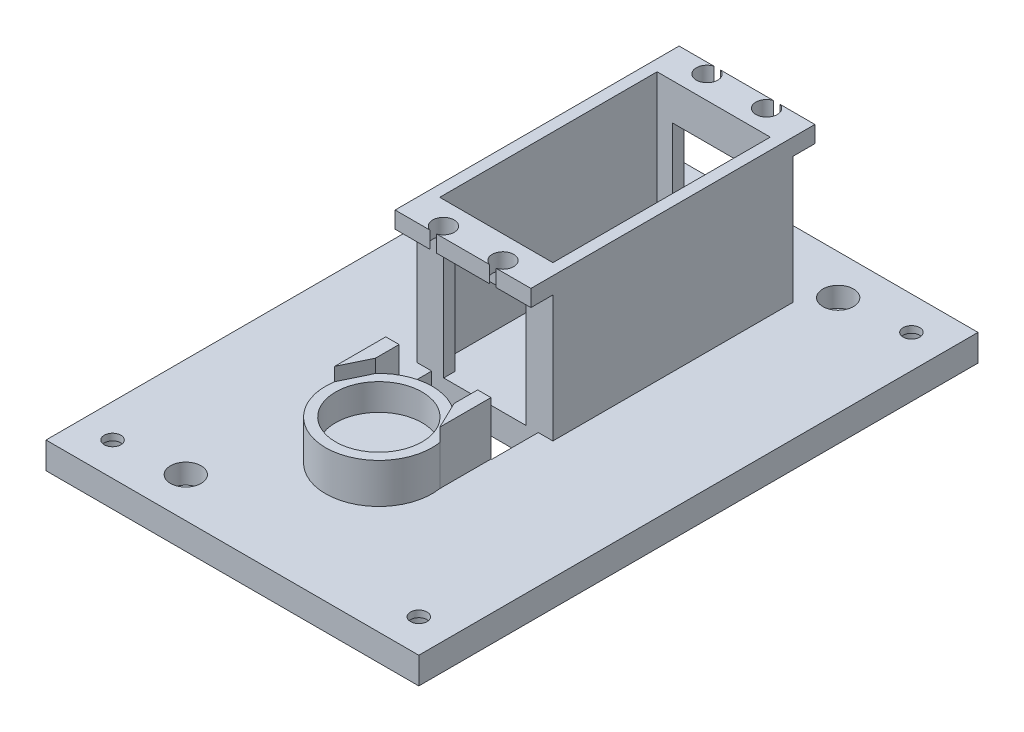
SolidWorks part; units mm, degrees
other "Markup1"
sketch "Sketch13" plane through (63.4306, 35.56, -46.9233) normal (0.8871, 0.4534, -0.0863) x (0.4601, -0.8836, 0.0876)
sketch "Sketch14" plane through (63.4306, 35.56, -46.9233) normal (0.8871, 0.4534, -0.0863) x (0.4601, -0.8836, 0.0876)
sketch "Sketch18" plane through (63.4306, 35.56, -46.9233) normal (0.8871, 0.4534, -0.0863) x (0.4601, -0.8836, 0.0876)
sketch "Sketch19" plane through (63.4306, 35.56, -46.9233) normal (0.8871, 0.4534, -0.0863) x (0.4601, -0.8836, 0.0876)
sketch "Sketch20" plane through (63.4306, 35.56, -46.9233) normal (0.8871, 0.4534, -0.0863) x (0.4601, -0.8836, 0.0876)
sketch "Sketch21" plane through (63.4306, 35.56, -46.9233) normal (0.8871, 0.4534, -0.0863) x (0.4601, -0.8836, 0.0876)
sketch "Sketch22" plane through (63.4306, 33.655, -46.9233) normal (0.8871, 0.4534, -0.0863) x (0.4601, -0.8836, 0.0876)
ref_plane "Front Plane" through (0, 0, 0) normal (0, 0, 1) x (1, 0, 0)
ref_plane "Top Plane" through (0, 0, 0) normal (0, 1, 0) x (1, 0, 0)
ref_plane "Right Plane" through (0, 0, 0) normal (1, 0, 0) x (0, 0, -1)
sketch "Sketch1" plane through (56.4019, 0, 2.6132) normal (0, 1, 0) x (1, 0, 0)
  line L1 (-64.0913, -57.1435) -> (7.0287, -57.1435)
  line L2 (-64.0913, -57.1435) -> (-64.0913, 49.5365)
  line L3 (-64.0913, 49.5365) -> (7.0287, 49.5365)
  line L4 (7.0287, -57.1435) -> (7.0287, 49.5365)
  dimension "D1" = 71.12
  dimension "D2" = 106.68
extrude "Boss-Extrude1" add sketch "Sketch1" along normal blind 5.08
sketch "Sketch3" plane through (56.4019, 5.08, 2.6132) normal (0, 1, 0) x (1, 0, 0)
  line L1 (-17.7363, 34.6775) -> (-39.3263, 34.6775)
  line L2 (-17.7363, 34.6775) -> (-17.7363, -6.8007)
  line L3 (-17.7363, -6.8007) -> (-39.3263, -6.8007)
  line L4 (-39.3263, 34.6775) -> (-39.3263, -6.8007)
  line L5 (-41.4853, 36.8365) -> (-15.5773, 36.8365)
  line L6 (-41.4853, 36.8365) -> (-41.4853, -8.9597)
  line L7 (-41.4853, -8.9597) -> (-15.5773, -8.9597)
  line L8 (-15.5773, 36.8365) -> (-15.5773, -8.9597)
  line L9 (7.0287, 49.5365) -> (-64.0913, 49.5365) construction
  point P5 (-28.5313, 36.8365)
  point P8 (-28.5313, 49.5365)
  dimension "D1" = 21.59
  dimension "D2" = 41.4782
  dimension "D4" = 2.159
  dimension "D5" = 2.159
  dimension "D6" = 2.159
  dimension "D7" = 2.159
  dimension "D8" = 12.7
extrude "Boss-Extrude2" add sketch "Sketch3" along normal blind 24.13
sketch "Sketch4" plane through (0, 29.21, 0) normal (0, 1, 0) x (1, 0, 0)
  line L0 (40.8246, -11.5729) -> (40.8246, 34.2233) construction
  line L1 (17.0756, 32.0643) -> (38.6656, 32.0643)
  line L2 (17.0756, 32.0643) -> (17.0756, -9.4139)
  line L3 (17.0756, -9.4139) -> (38.6656, -9.4139)
  line L4 (38.6656, 32.0643) -> (38.6656, -9.4139)
  line L5 (14.9166, 38.4143) -> (40.8246, 38.4143)
  line L6 (14.9166, 38.4143) -> (14.9166, -15.7639)
  line L7 (14.9166, -15.7639) -> (40.8246, -15.7639)
  line L8 (40.8246, 38.4143) -> (40.8246, -15.7639)
  line L10 (14.9166, 34.2233) -> (14.9166, -11.5729) construction
  dimension "D1" = 6.35
  dimension "D2" = 6.35
extrude "Boss-Extrude3" add sketch "Sketch4" along normal blind 3.175
sketch "Sketch5" plane through (0, 32.385, 0) normal (0, 1, 0) x (1, 0, 0)
  line L0 (40.8246, -15.7639) -> (40.8246, 38.4143) construction
  line L2 (27.8706, 32.0643) -> (27.8706, 42.675) construction
  line L3 (38.6656, 32.0643) -> (17.0756, 32.0643) construction
  circle A0 centre (22.1937, 36.4712) radius 2.0497
  circle A1 centre (33.5475, 36.4712) radius 2.0497
  circle A2 centre (22.1937, -13.8208) radius 2.0497
  circle A3 centre (33.5475, -13.8208) radius 2.0497
  point P10 (40.8246, 11.3252)
  dimension "D1" = 4.0994
  dimension "D5" = 5.6769
  dimension "D2" = 11.3538
  dimension "D3" = 11.3538
  dimension "D4" = 5.6769
  dimension "D6" = 50.292
  dimension "D7" = 25.146
extrude "Cut-Extrude1" cut sketch "Sketch5" against normal blind 3.175
sketch "Sketch7" plane through (0, 0, -34.2233) normal (0, 0, -1) x (-1, 0, 0)
  line L0 (-40.8246, 5.08) -> (-14.9166, 5.08) construction
  line L1 (-35.7446, 5.08) -> (-19.9966, 5.08)
  line L2 (-35.7446, 5.08) -> (-35.7446, 25.4)
  line L3 (-35.7446, 25.4) -> (-19.9966, 25.4)
  line L4 (-19.9966, 5.08) -> (-19.9966, 25.4)
  line L5 (-40.8246, 29.21) -> (-40.8246, 5.08) construction
  line L6 (-14.9166, 29.21) -> (-14.9166, 5.08) construction
  dimension "D1" = 5.08
  dimension "D2" = 5.08
  dimension "D3" = 20.32
extrude "Cut-Extrude3" cut sketch "Sketch7" against normal up to surface (45.7962 mm away) up to face at (27.8706, 17.145, 11.5729)
sketch "Sketch8" plane through (0, 5.08, 0) normal (0, 1, 0) x (1, 0, 0)
  line L0 (63.4306, 46.9233) -> (-7.6894, 46.9233) construction
  circle A0 centre (27.8706, -31.8167) radius 10.16
  point P4 (27.8706, 46.9233)
  dimension "D1" = 20.32
  dimension "D2" = 78.74
extrude "Boss-Extrude4" add sketch "Sketch8" along normal blind 7.62
sketch "Sketch9" plane through (0, 12.7, 0) normal (0, 1, 0) x (1, 0, 0)
  circle A0 centre (27.8706, -31.8167) radius 8.255
  dimension "D1" = 16.51
extrude "Cut-Extrude4" cut sketch "Sketch9" against normal blind 5.08 contours A0
sketch "Sketch10" plane through (0, 5.08, 0) normal (0, 1, 0) x (1, 0, 0)
  line L1 (17.7106, -11.5729) -> (38.0306, -11.5729)
  line L2 (17.7106, -11.5729) -> (17.7106, -20.4629)
  line L3 (17.7106, -20.4629) -> (38.0306, -20.4629)
  line L4 (38.0306, -11.5729) -> (38.0306, -20.4629)
  line L5 (63.4306, 46.9233) -> (-7.6894, 46.9233) construction
  line L6 (35.7446, -11.5729) -> (40.8246, -11.5729) construction
  point P8 (27.8706, -11.5729)
  point P9 (27.8706, 46.9233)
  dimension "D1" = 20.32
  dimension "D3" = 8.89
extrude "Cut-Extrude5" cut sketch "Sketch10" against normal through all
sketch "Sketch11" plane through (0, 5.08, 0) normal (0, 1, 0) x (1, 0, 0)
  line L0 (63.4306, 46.9233) -> (-7.6894, 46.9233) construction
  line L1 (-7.6894, -59.7567) -> (63.4306, -59.7567) construction
  line L2 (63.4306, -59.7567) -> (63.4306, 46.9233) construction
  line L3 (-7.6894, 46.9233) -> (-7.6894, -59.7567) construction
  circle A0 centre (44.3806, 39.3033) radius 1.5875
  circle A1 centre (11.3606, -52.1367) radius 1.5875
  dimension "D1" = 3.175
  dimension "D2" = 3.175
  dimension "D3" = 7.62
  dimension "D4" = 7.62
  dimension "D5" = 19.05
  dimension "D6" = 19.05
extrude "Cut-Extrude6" cut sketch "Sketch11" against normal through all
sketch "Sketch15" plane through (0, 5.08, 0) normal (0, 1, 0) x (1, 0, 0)
  circle A0 centre (11.3606, -52.1367) radius 2.921
  circle A1 centre (44.3806, 39.3033) radius 2.921
  dimension "D1" = 5.842
  dimension "D2" = 5.842
extrude "Cut-Extrude7" cut sketch "Sketch15" against normal blind 3.81
sketch "Sketch16" plane through (0, 0, 0) normal (0, -1, 0) x (1, 0, 0)
  line L0 (-7.6894, 59.7567) -> (63.4306, 59.7567) construction
  line L1 (-7.6894, -46.9233) -> (-7.6894, 59.7567) construction
  circle A0 centre (-1.3394, 53.4067) radius 2.921
  circle A1 centre (57.0806, 53.4067) radius 2.921
  circle A2 centre (57.0806, -40.5733) radius 2.921
  circle A3 centre (-1.3394, -40.5733) radius 2.921
  dimension "D1" = 6.35
  dimension "D5" = 5.842
  dimension "D2" = 6.35
  dimension "D3" = 2
  dimension "D4" = 2
extrude "Cut-Extrude8" cut sketch "Sketch16" against normal blind 3.81
sketch "Sketch17" plane through (0, 0, 0) normal (0, -1, 0) x (1, 0, 0)
  circle A0 centre (-1.3394, 53.4067) radius 1.5875
  circle A1 centre (57.0806, 53.4067) radius 1.5875
  circle A2 centre (57.0806, -40.5733) radius 1.5875
  circle A3 centre (-1.3394, -40.5733) radius 1.5875
  dimension "D1" = 2
  dimension "D3" = 3.175
  dimension "D2" = 2
extrude "Cut-Extrude9" cut sketch "Sketch17" against normal through all
sketch "Sketch23" plane through (0, 5.08, 0) normal (0, 1, 0) x (1, 0, 0)
  line L0 (17.7106, -20.4629) -> (38.0306, -20.4629) construction
  line L1 (20.3776, -20.4629) -> (17.8376, -20.4629)
  line L2 (20.3776, -20.4629) -> (20.3776, -24.9552)
  line L4 (17.8376, -20.4629) -> (17.8376, -30.2153)
  line L5 (17.8376, -30.2153) -> (20.3776, -24.9552)
  line L6 (35.3636, -20.4629) -> (37.9036, -20.4629)
  line L7 (35.3636, -20.4629) -> (35.3636, -24.9552)
  line L9 (37.9036, -20.4629) -> (37.9036, -30.2153)
  line L10 (35.3636, -24.9552) -> (37.9036, -30.2153)
  circle A2 centre (27.8706, -31.8167) radius 10.16 construction
  circle A3 centre (27.8706, -31.8167) radius 10.16 construction
  point P1 (17.7106, -31.8167)
  point P9 (20.3776, -24.9552)
  point P11 (35.3636, -24.9552)
  point P12 (37.9036, -30.2153)
  point P14 (27.8706, -20.4629)
  point P19 (37.9036, -30.2153)
  dimension "D1" = 14.986
  dimension "D2" = 7.493
  dimension "D3" = 2.54
  dimension "D4" = 2.54
extrude "Boss-Extrude5" add sketch "Sketch23" along normal blind 10.16
